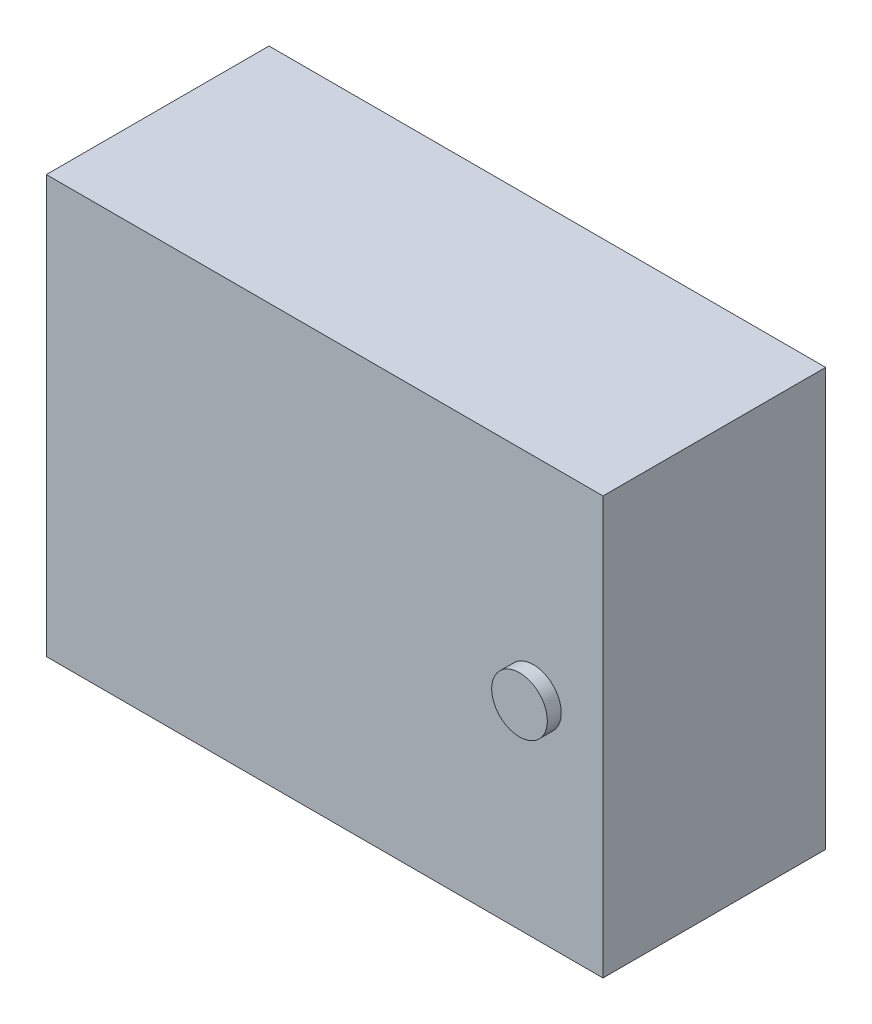
SolidWorks part; units mm, degrees
ref_plane "Front Plane" through (0, 0, 0) normal (0, 0, 1) x (1, 0, 0)
ref_plane "Top Plane" through (0, 0, 0) normal (0, 1, 0) x (1, 0, 0)
ref_plane "Right Plane" through (0, 0, 0) normal (1, 0, 0) x (0, 0, -1)
sketch "Sketch1" plane through (0, 0, 0) normal (0, 0, 1) x (1, 0, 0)
  line L1 (-200, -150) -> (200, -150)
  line L2 (-200, -150) -> (-200, 150)
  line L3 (-200, 150) -> (200, 150)
  line L4 (200, -150) -> (200, 150)
  line L5 (-200, -150) -> (200, 150) construction
  line L6 (-200, 150) -> (200, -150) construction
  point P0 (0, 0)
  dimension "D1" = 400
  dimension "D2" = 300
extrude "Boss-Extrude1" add sketch "Sketch1" along normal blind 160
sketch "Sketch2" plane through (0, 0, 160) normal (0, 0, 1) x (1, 0, 0)
  line L0 (0, 0) -> (150, 0) construction
  circle A0 centre (150, 0) radius 20
  dimension "D2" = 40
  dimension "D1" = 150
extrude "Boss-Extrude2" add sketch "Sketch2" along normal blind 10
